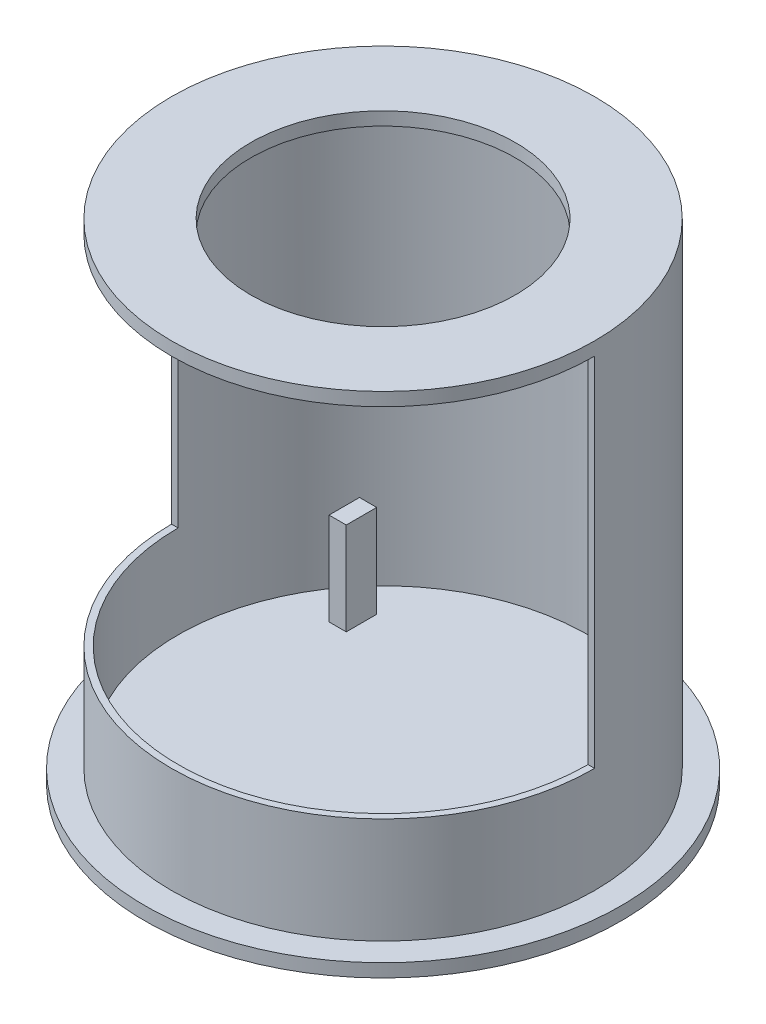
SolidWorks part; units mm, degrees
ref_plane "Plan de face" through (0, 0, 0) normal (0, 0, 1) x (1, 0, 0)
ref_plane "Plan de dessus" through (0, 0, 0) normal (0, 1, 0) x (1, 0, 0)
ref_plane "Plan de droite" through (0, 0, 0) normal (1, 0, 0) x (0, 0, -1)
sketch "Esquisse1" plane through (0, 0, 0) normal (0, 1, 0) x (1, 0, 0)
  line L0 (-80, 0) -> (-77.5, 0)
  line L1 (-77.5, 0) -> (0, 0)
  line L2 (0, 0) -> (77.5, 0)
  circle A0 centre (0, 0) radius 80
  circle A1 centre (0, 0) radius 77.5
  arc A2 (77.5, 0) -> (0, 77.5) centre (0, 0) ccw
  arc A3 (0, 80) -> (-80, 0) centre (0, 0) ccw
  arc A4 (0, 80) -> (80, 0) centre (0, 0) cw
  arc A5 (80, 0) -> (0, 80) centre (0, 0) ccw
  point P10 (0, 0)
  point P12 (0, 0)
  dimension "D1" = 160
  dimension "D2" = 155
  dimension "D3" = 80
extrude "Boss.-Extru.1" add sketch "Esquisse1" along normal blind 5 contours L2 A1 L1
sketch "Esquisse2" plane through (0, 0, 0) normal (0, -1, 0) x (1, 0, 0)
  line L0 (0, 0) -> (77.5, 0)
  line L1 (-77.5, 0) -> (77.5, 0) construction
  line L2 (0, 0) -> (-77.5, 0)
  line L3 (-80, 0) -> (80, 0)
  arc A0 (-77.5, 0) -> (77.5, 0) centre (0, 0) ccw construction
  circle A1 centre (0, 0) radius 77.5
  arc A2 (77.5, 0) -> (-77.5, 0) centre (0, 0) cw
  arc A3 (80, 0) -> (-80, 0) centre (0, 0) cw
  arc M2 (-77.5, 0) -> (77.5, 0) centre (0, 0) ccw
  dimension "D1" = 80
extrude "Boss.-Extru.2" add sketch "Esquisse2" against normal blind 180 contours A3 L3 M2
sketch "Esquisse4" plane through (0, 180, 0) normal (0, 1, 0) x (1, 0, 0)
  line L0 (-77.5, 0) -> (77.5, 0)
  arc A0 (77.5, 0) -> (-77.5, 0) centre (0, 0) ccw
  arc A1 (77.5, 0) -> (-77.5, 0) centre (0, 0) ccw construction
extrude "Boss.-Extru.3" add sketch "Esquisse4" against normal blind 5
sketch "Esquisse5" plane through (0, 180, 0) normal (0, 1, 0) x (1, 0, 0)
  line L0 (-80, 0) -> (80, 0) construction
  line L1 (-50, 0) -> (50, 0)
  arc A0 (50, 0) -> (-50, 0) centre (0, 0) ccw
  dimension "D1" = 50
extrude "Enlèv. mat.-Extru.1" cut sketch "Esquisse5" against normal blind 5
sketch "Esquisse6" plane through (0, 0, 0) normal (0, 1, 0) x (1, 0, 0)
  line L0 (0, 0) -> (80, 0)
  line L1 (0, 0) -> (-80, 0)
  line L2 (0, 0) -> (77.5, 0)
  line L3 (-77.5, 0) -> (0, 0)
  arc A0 (80, 0) -> (-80, 0) centre (0, 0) cw
  arc A3 (77.5, 0) -> (-77.5, 0) centre (0, 0) cw
  dimension "D1" = 77.5
  dimension "D2" = 77.5
extrude "Boss.-Extru.4" add sketch "Esquisse6" along normal blind 40 contours L0 A3 L1 A0
sketch "Esquisse7" plane through (0, 0, 0) normal (0, 1, 0) x (1, 0, 0)
  line L0 (0, 0) -> (-77.5, 0)
  line L1 (0, 0) -> (77.5, 0)
  arc A0 (-77.5, 0) -> (77.5, 0) centre (0, 0) ccw construction
  arc A1 (-77.5, 0) -> (77.5, 0) centre (0, 0) ccw
extrude "Boss.-Extru.5" add sketch "Esquisse7" along normal blind 5
sketch "Esquisse8" plane through (0, 0, 0) normal (0, -1, 0) x (1, 0, 0)
  circle A0 centre (0, 0) radius 90
  dimension "D1" = 180
extrude "Boss.-Extru.6" add sketch "Esquisse8" along normal blind 5
sketch "Esquisse9" plane through (0, 180, 0) normal (0, 1, 0) x (1, 0, 0)
  line L0 (0, 0) -> (80, 0)
  line L1 (50, 0) -> (80, 0) construction
  line L2 (0, 0) -> (77.5, 0)
  line L3 (0, 0) -> (-77.5, 0)
  line L4 (0, 0) -> (-80, 0)
  line L5 (0, 0) -> (-77.5, 0)
  line L6 (0, 0) -> (-80, 0)
  line L7 (-77.5, 0) -> (-80, 0)
  line L8 (77.5, 0) -> (80, 0)
  circle A0 centre (0, 0) radius 80 construction
  circle A1 centre (0, 0) radius 77.5 construction
  arc A2 (80, 0) -> (-80, 0) centre (0, 0) cw
  arc A3 (77.5, 0) -> (-77.5, 0) centre (0, 0) cw
  line M1 (-80, 0) -> (-50, 0)
extrude "Boss.-Extru.7" add sketch "Esquisse9" against normal blind 5 separate body contours L0 A3 A2 M1
sketch "Esquisse10" plane through (0, 180, 0) normal (0, 1, 0) x (1, 0, 0)
  line L0 (77.5, 0) -> (-77.5, 0)
  line L1 (-80, 0) -> (-50, 0) construction
  line L2 (0, 0) -> (-77.5, 0)
  line L3 (0, 0) -> (77.5, 0)
  line L4 (0, 0) -> (-50, 0)
  line L5 (0, 0) -> (50, 0)
  arc A0 (-77.5, 0) -> (77.5, 0) centre (0, 0) ccw construction
  arc A1 (-50, 0) -> (50, 0) centre (0, 0) ccw
  arc A2 (-77.5, 0) -> (77.5, 0) centre (0, 0) ccw
  line M1 (-80, 0) -> (-50, 0)
  line M3 (50, 0) -> (80, 0)
extrude "Boss.-Extru.8" add sketch "Esquisse10" against normal blind 5 contours A2 A1 M1 M3
sketch "Esquisse12" plane through (0, 5, 0) normal (0, 1, 0) x (1, 0, 0)
  line L0 (0, 0) -> (-77.5, 0)
  line L1 (0, 0) -> (77.5, 0)
  line L3 (53.17, 44.26) -> (46.67, 44.26)
  line L4 (53.17, 44.26) -> (53.17, 32.75)
  line L5 (53.17, 32.75) -> (46.67, 32.75)
  line L6 (46.67, 44.26) -> (46.67, 32.75)
  line L7 (-53.17, 32.75) -> (-46.67, 32.75)
  line L8 (-53.17, 32.75) -> (-53.17, 44.2582)
  line L9 (-53.17, 44.2582) -> (-46.67, 44.2582)
  line L10 (-46.67, 32.75) -> (-46.67, 44.2582)
  circle A0 centre (0, 0) radius 77.5 construction
  dimension "D1" = 6.5
  dimension "D2" = 6.5
  dimension "D3" = 11.51
  dimension "D4" = 11.5082
  dimension "D5" = 53.17
  dimension "D6" = 53.17
  dimension "D7" = 32.75
  dimension "D8" = 32.75
extrude "Boss.-Extru.9" add sketch "Esquisse12" along normal up to vertex (35 mm away) contours L7 L10 L9 L8 | L4 L5 L6 L3
